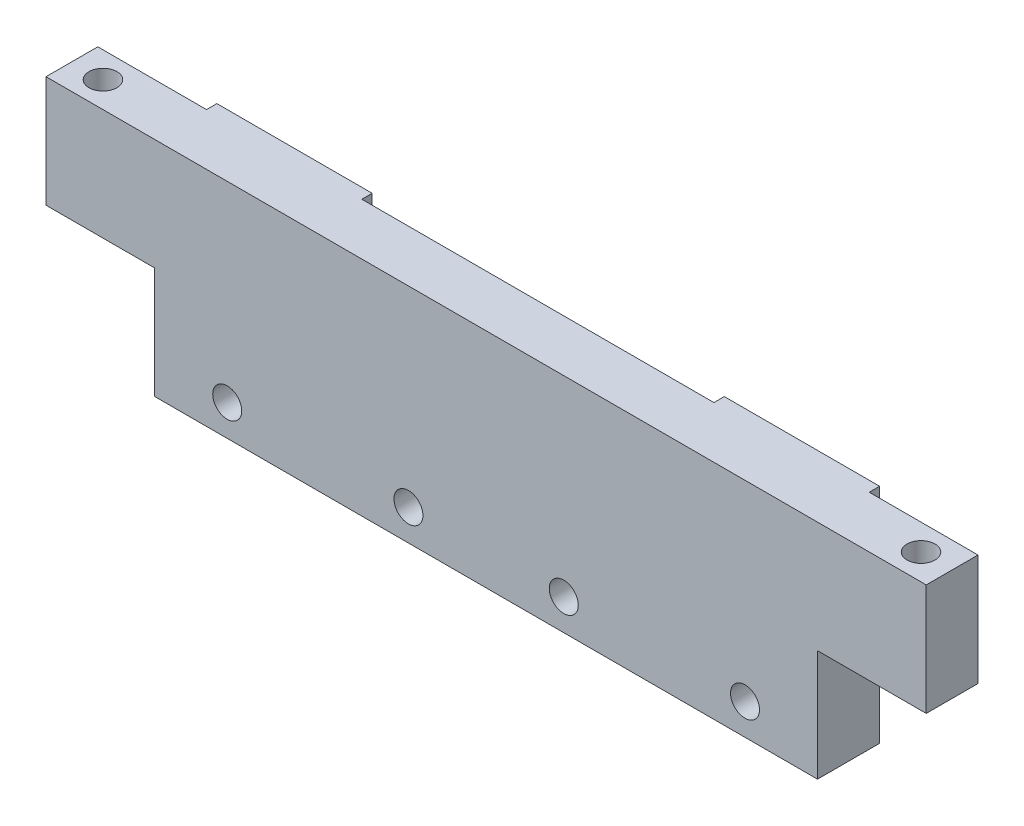
SolidWorks part; units mm, degrees
ref_plane "Front Plane" through (0, 0, 0) normal (0, 0, 1) x (1, 0, 0)
ref_plane "Top Plane" through (0, 0, 0) normal (0, 1, 0) x (1, 0, 0)
ref_plane "Right Plane" through (0, 0, 0) normal (1, 0, 0) x (0, 0, -1)
sketch "Sketch1" plane through (0, 0, 0) normal (0, 1, 0) x (1, 0, 0)
  line L0 (-39.5, 0) -> (39.5, 0) construction
  line L5 (42.5, -2.5) -> (-42.5, -2.5)
  line L6 (42.5, -2.5) -> (42.5, 2.5)
  line L7 (42.5, 2.5) -> (32, 2.5)
  line L8 (-42.5, -2.5) -> (-42.5, 2.5)
  line L9 (42.5, -2.5) -> (-42.5, 2.5) construction
  line L10 (42.5, 2.5) -> (-42.5, -2.5) construction
  line L11 (-32, 2.5) -> (-42.5, 2.5)
  line L13 (-32, 2.5) -> (-32, 3.5)
  line L14 (-32, 3.5) -> (-17, 3.5)
  line L15 (-17, 2.5) -> (-17, 3.5)
  line L17 (32, 2.5) -> (32, 3.5)
  line L18 (32, 3.5) -> (17, 3.5)
  line L19 (17, 2.5) -> (17, 3.5)
  line L20 (17, 2.5) -> (-17, 2.5)
  circle A0 centre (-39.5, 0) radius 1.35
  circle A1 centre (39.5, 0) radius 1.35
  point P0 (0, 0)
  point P18 (-24.5, 3.5)
  point P19 (24.5, 3.5)
  dimension "D3" = 2.7
  dimension "D1" = 85
  dimension "D2" = 79
  dimension "D4" = 5
  dimension "D5" = 1
  dimension "D6" = 15
  dimension "D7" = 15
  dimension "D8" = 15
extrude "Boss-Extrude1" add sketch "Sketch1" along normal blind 21.5
sketch "Sketch2" plane through (0, 0, 2.5) normal (0, 0, -1) x (-1, 0, 0)
  line L0 (-17, 21.5) -> (17, 21.5) construction
  line L2 (-42.5, 21.5) -> (-42.5, 0) construction
  circle A0 centre (-7.5, 3) radius 1.4
  circle A1 centre (7.5, 3) radius 1.4
  circle A2 centre (-25, 3) radius 1.4
  circle A3 centre (25, 3) radius 1.4
  point P12 (0, 0)
  point P13 (0, 0)
  dimension "D2" = 2.8
  dimension "D1" = 18.5
  dimension "D3" = 17.5
  dimension "D4" = 35
  dimension "D5" = 50
  dimension "D6" = 67.5
extrude "Cut-Extrude1" cut sketch "Sketch2" along normal blind 21.5 contours A2 | A0 | A1 | A3
sketch "Sketch3" plane through (0, 0, -2.5) normal (0, 0, -1) x (-1, 0, 0)
  line L0 (-32, 21.5) -> (-32, 0) construction
  line L1 (-32, 10.75) -> (-42.5, 10.75)
  line L2 (-32, 10.75) -> (-32, 0)
  line L3 (-32, 0) -> (-42.5, 0)
  line L4 (-42.5, 10.75) -> (-42.5, 0)
  line L5 (32, 21.5) -> (32, 0) construction
  line L6 (32, 10.75) -> (42.5, 10.75)
  line L7 (32, 10.75) -> (32, 0)
  line L8 (32, 0) -> (42.5, 0)
  line L9 (42.5, 10.75) -> (42.5, 0)
  line L10 (42.5, 21.5) -> (42.5, 0) construction
extrude "Cut-Extrude2" cut sketch "Sketch3" against normal through all both
